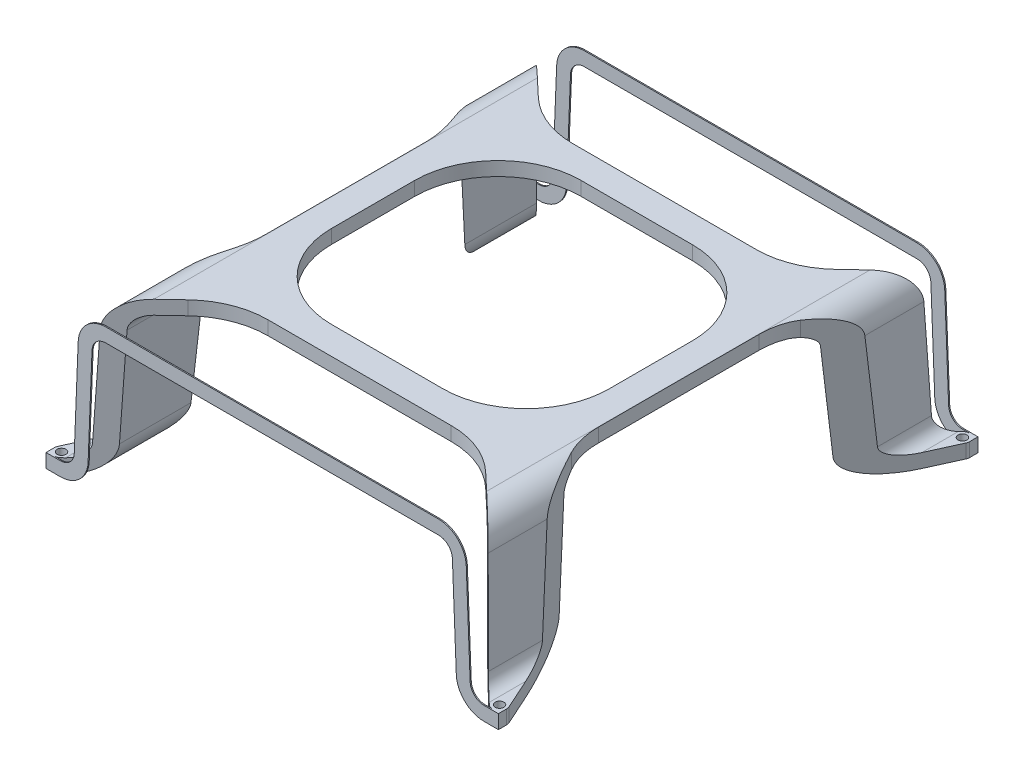
SolidWorks part; units mm, degrees
material "ABS"
ref_plane "Plan de face" through (0, 0, 0) normal (0, 0, 1) x (1, 0, 0)
ref_plane "Plan de dessus" through (0, 0, 0) normal (0, 1, 0) x (1, 0, 0)
ref_plane "Plan de droite" through (0, 0, 0) normal (1, 0, 0) x (0, 0, -1)
sketch "Esquisse1" plane through (0, 0, 0) normal (0, 0, 1) x (1, 0, 0)
  line L0 (-81.5974, 0) -> (81.5974, 0) construction
  line L3 (-81.5974, 0) -> (-76.4026, 0)
  line L4 (-81.5974, 0) -> (-81.5974, 5)
  line L5 (-81.5974, 5) -> (-76.4026, 5)
  line L6 (81.5974, 0) -> (81.5974, 5)
  line L7 (-71.4066, 9.8015) -> (-69.9921, 45.3971)
  line L9 (69.9921, 45.3971) -> (71.4066, 9.8015)
  line L11 (76.4026, 5) -> (81.5974, 5)
  line L13 (-60, 50) -> (60, 50)
  line L16 (-64.9961, 45.1985) -> (-66.4105, 9.6029)
  line L17 (64.9961, 45.1985) -> (66.4105, 9.6029)
  line L18 (76.4026, 0) -> (81.5974, 0)
  line L19 (-60, 55) -> (60, 55)
  arc A0 (60, 50) -> (64.9961, 45.1985) centre (60, 45) cw
  arc A3 (-64.9961, 45.1985) -> (-60, 50) centre (-60, 45) cw
  arc A4 (71.4066, 9.8015) -> (76.4026, 5) centre (76.4026, 10) ccw
  arc A7 (-71.4066, 9.8015) -> (-76.4026, 5) centre (-76.4026, 10) cw
  arc A8 (66.4105, 9.6029) -> (76.4026, 0) centre (76.4026, 10) ccw
  arc A9 (-66.4105, 9.6029) -> (-76.4026, 0) centre (-76.4026, 10) cw
  arc A10 (69.9921, 45.3971) -> (60, 55) centre (60, 45) ccw
  arc A11 (-60, 55) -> (-69.9921, 45.3971) centre (-60, 45) ccw
  point P3 (0, 0)
  point P15 (-79, 5)
  point P16 (79, 5)
  point P21 (66.7921, 0)
  point P27 (71.5974, 5)
  point P31 (0, 0)
  point P32 (0, 0)
  point P33 (0, 50)
  point P36 (-71.5974, 5)
  point P38 (-44.5242, 50.3282)
  point P39 (-34.8581, 29.07)
  point P40 (-39.8292, 28.3262)
  point P41 (0, 0)
  point P42 (0, 0)
  point P43 (-39.8292, 32.255)
  point P44 (-39.8292, 47.3256)
  point P45 (0, 0)
  dimension "D9" = 5
  dimension "D10" = 5
  dimension "D6" = 10
  dimension "D5" = 10
  dimension "D13" = 5
  dimension "D14" = 120
  dimension "D2" = 5
  dimension "D3" = 10
  dimension "D4" = 10
  dimension "D7" = 5
  dimension "D8" = 5
  dimension "D11" = 5
  dimension "D12" = 158
  dimension "D15" = 50
extrude "Boss.-Extru.1" add sketch "Esquisse1" along normal blind 173
hole_wizard "Dégagement M31" positions "Esquisse2" profile "Esquisse3" hole size "M3" standard "ISO"
sketch "Esquisse2" plane through (0, 5, 0) normal (0, 1, 0) x (1, 0, 0)
  line L1 (79, -170) -> (-79, -170)
  line L2 (79, -170) -> (79, -3)
  line L3 (79, -3) -> (-79, -3)
  line L4 (-79, -170) -> (-79, -3)
  line L5 (79, -170) -> (-79, -3) construction
  line L6 (79, -3) -> (-79, -170) construction
  line L7 (-81.5974, -173) -> (81.5974, 0) construction
  point P0 (-79, -170)
  point P2 (-79, -3)
  point P4 (79, -170)
  point P6 (79, -3)
  point P87 (73.5138, -42.4914)
  point P88 (0, -86.5)
  point P89 (0, -86.5)
  dimension "D1" = 167
  dimension "D2" = 158
sketch "Esquisse3" plane through (-79, 5, 170) normal (1, 0, 0) x (0, 0, 1)
  line L0 (0, 0) -> (0, 5.9614)
  line L1 (0, 5.9614) -> (1.6, 5)
  line L2 (1.6, 5) -> (1.6, 0)
  line L5 (1.6, 0) -> (0, 0)
  line L10 (0, 5.9614) -> (-1.6, 5) construction
  line L11 (0, -6.35) -> (0, 107.95) construction
  dimension "Diamètre du perçage" = 3.2
  dimension "Profondeur du perçage" = 5
  dimension "Angle de pointe" = 118
sketch "Esquisse4" plane through (0, 55, 0) normal (0, 1, 0) x (1, 0, 0)
  line L0 (55.0931, -136.5) -> (-55.0931, -86.5) construction
  line L1 (-55.0931, -86.5) -> (55.0931, -36.5) construction
  line L2 (55.0931, -136.5) -> (55.0931, -36.5) construction
  line L3 (0, -172.5974) -> (0, 0) construction
  line L7 (-81.3663, -168.9289) -> (-62.7625, -127.8287)
  line L10 (60.0931, -115.4577) -> (60.0931, -57.5423)
  line L13 (-55.0931, -86.5) -> (-81.5974, -86.5) construction
  line L19 (-60.0931, -115.4577) -> (-60.0931, -57.5423)
  line L20 (-62.7625, -45.1713) -> (-81.3663, -4.0711)
  line L21 (-77.2178, -171.8894) -> (-53.6685, -149.6766)
  line L22 (-81.5974, -170) -> (-81.5974, -3)
  line L23 (-33.0836, -141.5) -> (33.0836, -141.5)
  line L24 (53.6685, -149.6766) -> (77.2178, -171.8894)
  line L25 (-81.5974, -173) -> (-81.5974, 0) construction
  line L26 (81.3663, -168.9289) -> (62.7625, -127.8287)
  line L27 (81.5974, -173) -> (81.5974, 0) construction
  line L30 (62.7625, -45.1713) -> (81.3663, -4.0711)
  line L31 (77.2178, -1.1106) -> (53.6685, -23.3234)
  line L32 (-79, -0.4026) -> (79, -0.4026)
  line L33 (33.0836, -31.5) -> (-33.0836, -31.5)
  line L34 (-53.6685, -23.3234) -> (-77.2178, -1.1106)
  line L35 (81.5974, -3) -> (81.5974, -170)
  line L36 (79, -170) -> (55.0931, -136.5) construction
  line L37 (-20.0931, -131.5) -> (20.0931, -131.5)
  line L38 (-50.0931, -101.5) -> (-50.0931, -71.5)
  line L39 (-20.0931, -41.5) -> (20.0931, -41.5)
  line L40 (50.0931, -101.5) -> (50.0931, -71.5)
  line L41 (55.0931, -36.5) -> (79, -3) construction
  line L42 (-55.0931, -86.5) -> (-79, -170) construction
  line L43 (-55.0931, -86.5) -> (-79, -3) construction
  line L44 (79, -172.5974) -> (-79, -172.5974)
  line L45 (-79, -172.5974) -> (-81.5974, -172.5974)
  line L46 (-81.5974, -172.5974) -> (-81.5974, -170)
  line L47 (-81.5974, -3) -> (-81.5974, -0.4026)
  line L48 (-81.5974, -0.4026) -> (-79, -0.4026)
  line L49 (79, -0.4026) -> (81.5974, -0.4026)
  line L50 (81.5974, -0.4026) -> (81.5974, -3)
  line L51 (81.5974, -170) -> (81.5974, -172.5974)
  line L52 (81.5974, -172.5974) -> (79, -172.5974)
  circle A0 centre (55.0931, -136.5) radius 3.5 construction
  circle A1 centre (55.0931, -36.5) radius 3.5 construction
  circle A2 centre (-55.0931, -86.5) radius 3.5 construction
  arc A9 (-81.3663, -168.9289) -> (-77.2178, -171.8894) centre (-79, -170) ccw
  arc A10 (-77.2178, -1.1106) -> (-81.3663, -4.0711) centre (-79, -3) ccw
  arc A11 (81.3663, -4.0711) -> (77.2178, -1.1106) centre (79, -3) ccw
  arc A12 (77.2178, -171.8894) -> (81.3663, -168.9289) centre (79, -170) ccw
  arc A13 (53.6685, -23.3234) -> (33.0836, -31.5) centre (33.0836, -1.5) cw
  arc A14 (62.7625, -127.8287) -> (60.0931, -115.4577) centre (90.0931, -115.4577) cw
  arc A15 (60.0931, -57.5423) -> (62.7625, -45.1713) centre (90.0931, -57.5423) cw
  arc A16 (-62.7625, -127.8287) -> (-60.0931, -115.4577) centre (-90.0931, -115.4577) ccw
  arc A17 (-60.0931, -57.5423) -> (-62.7625, -45.1713) centre (-90.0931, -57.5423) ccw
  arc A18 (-33.0836, -31.5) -> (-53.6685, -23.3234) centre (-33.0836, -1.5) cw
  arc A19 (-53.6685, -149.6766) -> (-33.0836, -141.5) centre (-33.0836, -171.5) cw
  arc A20 (33.0836, -141.5) -> (53.6685, -149.6766) centre (33.0836, -171.5) cw
  arc A21 (20.0931, -131.5) -> (50.0931, -101.5) centre (20.0931, -101.5) ccw
  arc A22 (20.0931, -41.5) -> (50.0931, -71.5) centre (20.0931, -71.5) cw
  arc A23 (-50.0931, -71.5) -> (-20.0931, -41.5) centre (-20.0931, -71.5) cw
  arc A24 (-20.0931, -131.5) -> (-50.0931, -101.5) centre (-20.0931, -101.5) cw
  point P4 (-60.9465, -110.2838)
  point P8 (0, 0)
  point P9 (0, 0)
  point P10 (20.9465, -32)
  point P11 (0, -141.5)
  point P14 (61.0964, -117.0306)
  point P15 (-59.1473, -87)
  point P19 (0, -111.5)
  point P20 (0, 0)
  point P23 (60.0931, -86.5)
  point P76 (45, -31.5)
  point P94 (-60.0931, -86.5)
  point P109 (-45, -31.5)
  line M108 (-60, 0) -> (-60, -173)
  line M110 (60, -173) -> (60, 0)
  dimension "D3" = 7
  dimension "D15" = 30
  dimension "D1" = 100
  dimension "D2" = 121
  dimension "D4" = 10
  dimension "D5" = 10
  dimension "D6" = 5
  dimension "D9" = 90
  dimension "D10" = 5
  dimension "D11" = 5
  dimension "D12" = 5
extrude "Enlèv. mat.-Extru.1" cut sketch "Esquisse4" against normal through all contours A24 L37 A21 L40 A22 L39 A23 L38 | A15 L10 A14 L26 A12 L35 A11 L30 | A18 L33 A13 L31 L32 L34 M110 M108 | A10 L34 L32 M108 | A11 L32 L31 M110 | L19 A17 L20 A10 L22 A9 L7 A16 | A20 L23 A19 L21 L44 L24 M108 M110 | A12 L24 L44 M110 | A9 L44 L21 M108
